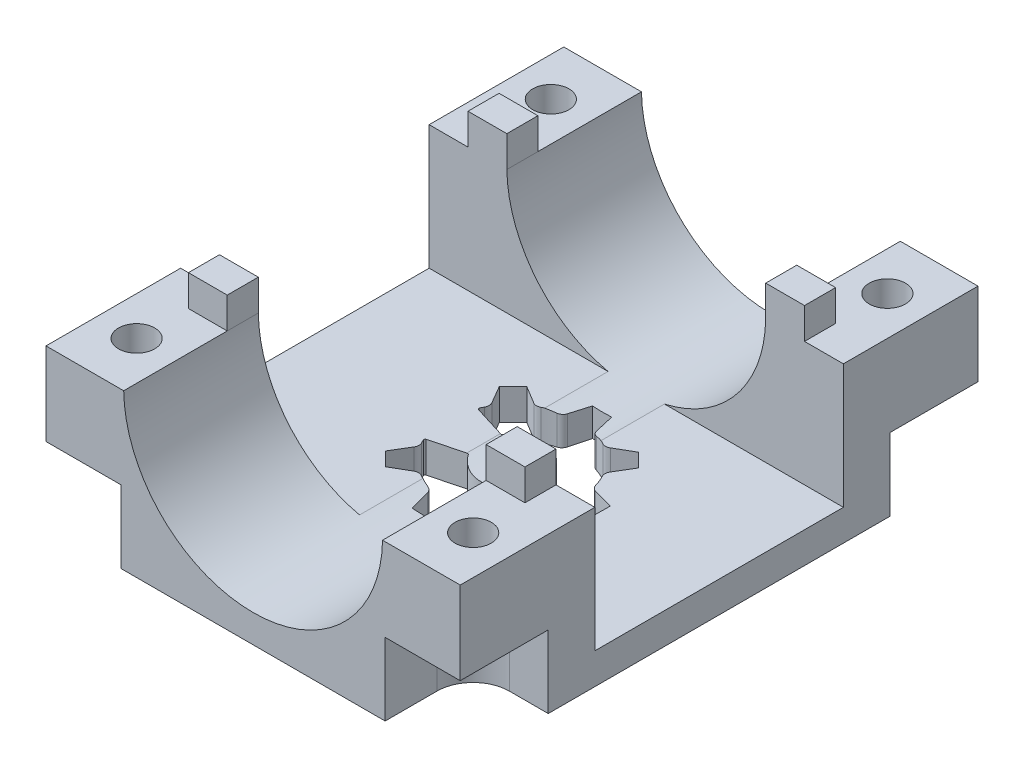
SolidWorks part; units mm, degrees
ref_plane "Alzado" through (0, 0, 0) normal (0, 0, 1) x (1, 0, 0)
ref_plane "Planta" through (0, 0, 0) normal (0, 1, 0) x (1, 0, 0)
ref_plane "Vista lateral" through (0, 0, 0) normal (1, 0, 0) x (0, 0, -1)
sketch "Croquis1" plane through (0, 0, 0) normal (0, 1, 0) x (1, 0, 0)
  line L1 (0, 0) -> (40, 0)
  line L2 (0, 0) -> (0, 50)
  line L3 (0, 50) -> (40, 50)
  line L4 (40, 0) -> (40, 50)
  dimension "D1" = 50
  dimension "D2" = 40
extrude "Saliente-Extruir1" add sketch "Croquis1" along normal blind 20
sketch "Croquis2" plane through (0, 0, 0) normal (0, 0, 1) x (1, 0, 0)
  line L1 (20, 20) -> (20, 20.2) construction
  line L2 (0, 20) -> (40, 20) construction
  circle A1 centre (20, 20.2) radius 12.5
  dimension "D1" = 0.2
  dimension "D2" = 25
extrude "Cortar-Extruir1" cut sketch "Croquis2" against normal through all
sketch "Croquis3" plane through (0, 20, 0) normal (0, 1, 0) x (1, 0, 0)
  line L1 (7.5016, 50) -> (0, 50) construction
  line L6 (0, 50) -> (0, 0) construction
  circle A0 centre (3.75, 45) radius 1.75
  circle A1 centre (36.25, 45) radius 1.75
  circle A2 centre (36.25, 5) radius 1.75
  circle A3 centre (3.75, 5) radius 1.75
  dimension "D1" = 5
  dimension "D5" = 3.5
  dimension "D2" = 3.75
  dimension "D3" = 2
  dimension "D4" = 2
extrude "Cortar-Extruir2" cut sketch "Croquis3" against normal through all
sketch "Croquis4" plane through (40, 0, 0) normal (1, 0, 0) x (0, 0, -1)
  line L2 (0, 20) -> (50, 20) construction
  line L3 (25, 20) -> (37, 20)
  line L4 (37, 20) -> (37, 8)
  line L5 (37, 8) -> (13, 8)
  line L6 (13, 8) -> (13, 20)
  line L7 (13, 20) -> (25, 20)
  dimension "D1" = 12
  dimension "D2" = 12
  dimension "D3" = 24
  dimension "D4" = 12
extrude "Cortar-Extruir3" cut sketch "Croquis4" against normal through all
sketch "Croquis5" plane through (0, 20, 0) normal (0, 1, 0) x (1, 0, 0)
  line L16 (7.5016, 40) -> (7.5016, 37)
  line L17 (3.7508, 37) -> (3.7508, 40)
  line L18 (0, 37) -> (7.5016, 37) construction
  line L19 (3.7508, 40) -> (7.5016, 40)
  line L21 (32.4984, 13) -> (32.4984, 10)
  line L22 (7.5016, 37) -> (3.7508, 37)
  line L23 (36.2492, 37) -> (36.2492, 40)
  line L24 (32.4984, 37) -> (40, 37) construction
  line L25 (36.2492, 40) -> (32.4984, 40)
  line L27 (7.5016, 13) -> (7.5016, 10)
  line L28 (32.4984, 37) -> (36.2492, 37)
  line L29 (36.2492, 13) -> (36.2492, 10)
  line L30 (32.4984, 13) -> (40, 13) construction
  line L31 (36.2492, 10) -> (32.4984, 10)
  line L33 (7.5016, 0) -> (7.5016, 13) construction
  line L34 (32.4984, 13) -> (36.2492, 13)
  line L35 (3.7508, 10) -> (3.7508, 13)
  line L36 (0, 13) -> (7.5016, 13) construction
  line L37 (3.7508, 13) -> (7.5016, 13)
  line L40 (7.5016, 10) -> (3.7508, 10)
  line L42 (32.4984, 40) -> (32.4984, 37)
  line L48 (7.5016, 37) -> (7.5016, 50) construction
  line L50 (32.4984, 50) -> (32.4984, 37) construction
  dimension "D1" = 3
  dimension "D4" = 3
extrude "Saliente-Extruir3" add sketch "Croquis5" along normal blind 3
sketch "Croquis6" plane through (0, 0, 0) normal (0, -1, 0) x (1, 0, 0)
  line L0 (20, 0) -> (20, -50) construction
  line L1 (13.1881, -19.6153) -> (14.5015, -18.2797)
  line L2 (18.9908, -16.3758) -> (20.864, -16.36)
  line L3 (25.3847, -18.1881) -> (26.7203, -19.5015)
  line L4 (28.6242, -23.9908) -> (28.64, -25.864)
  line L5 (26.8119, -30.3847) -> (25.4985, -31.7203)
  line L6 (14.2096, -27.5521) -> (17.384, -26.5714)
  line L7 (13.1881, -19.6153) -> (14.2199, -21.3215)
  line L8 (21.0092, -33.6242) -> (19.136, -33.64)
  line L9 (14.6153, -31.8119) -> (13.2797, -30.4985)
  line L10 (14.5015, -18.2797) -> (16.2249, -19.2826)
  line L11 (18.9908, -16.3758) -> (18.5139, -18.3118)
  line L12 (20.864, -16.36) -> (21.3734, -18.2878)
  line L13 (25.3847, -18.1881) -> (23.6785, -19.2199)
  line L14 (26.7203, -19.5015) -> (25.7174, -21.2249)
  line L15 (28.6242, -23.9908) -> (26.6882, -23.5139)
  line L16 (28.64, -25.864) -> (26.7122, -26.3734)
  line L17 (26.8119, -30.3847) -> (25.7801, -28.6785)
  line L18 (25.4985, -31.7203) -> (23.7751, -30.7174)
  line L19 (21.0092, -33.6242) -> (21.4861, -31.6882)
  line L20 (19.136, -33.64) -> (18.6266, -31.7122)
  line L21 (14.6153, -31.8119) -> (16.3215, -30.7801)
  line L22 (13.2797, -30.4985) -> (14.2826, -28.7751)
  line L23 (17.4066, -23.3915) -> (14.1706, -22.5477)
  line L24 (0, 0) -> (40, 0) construction
  line L26 (40, -50) -> (0, -50) construction
  line L27 (40, -25) -> (0, -25) construction
  line L28 (40, 0) -> (40, -50) construction
  line L29 (0, -50) -> (0, 0) construction
  arc A0 (21.9667, -31.1744) -> (23.0717, -30.7057) centre (20, -25) ccw
  arc A1 (14.127, -27.7383) -> (14.2943, -28.0717) centre (20, -25) ccw
  arc A2 (14.2096, -27.5521) -> (14.127, -27.7383) centre (14.2495, -27.6812) ccw
  arc A3 (14.0813, -22.3619) -> (14.1706, -22.5477) centre (14.2047, -22.4169) ccw
  arc A4 (16.9283, -19.2943) -> (16.2249, -19.2826) centre (16.587, -18.6603) cw
  arc A5 (14.2434, -22.0247) -> (14.2199, -21.3215) centre (13.6038, -21.6941) ccw
  arc A6 (21.8625, -18.7934) -> (21.3734, -18.2878) centre (22.0695, -18.1038) cw
  arc A7 (18.0333, -18.8256) -> (18.5139, -18.3118) centre (17.8148, -18.1396) ccw
  arc A8 (25.7057, -21.9283) -> (25.7174, -21.2249) centre (26.3397, -21.587) cw
  arc A9 (22.9753, -19.2434) -> (23.6785, -19.2199) centre (23.3059, -18.6038) ccw
  arc A10 (26.2066, -26.8625) -> (26.7122, -26.3734) centre (26.8962, -27.0695) cw
  arc A11 (26.1744, -23.0333) -> (26.6882, -23.5139) centre (26.8604, -22.8148) ccw
  arc A12 (23.0717, -30.7057) -> (23.7751, -30.7174) centre (23.413, -31.3397) cw
  arc A13 (25.7566, -27.9753) -> (25.7801, -28.6785) centre (26.3962, -28.3059) ccw
  arc A14 (18.1375, -31.2066) -> (18.6266, -31.7122) centre (17.9305, -31.8962) cw
  arc A15 (21.9667, -31.1744) -> (21.4861, -31.6882) centre (22.1852, -31.8604) ccw
  arc A16 (14.2943, -28.0717) -> (14.2826, -28.7751) centre (13.6603, -28.413) cw
  arc A17 (17.0247, -30.7566) -> (16.3215, -30.7801) centre (16.6941, -31.3962) ccw
  arc A18 (17.0247, -30.7566) -> (18.1375, -31.2066) centre (20, -25) ccw
  arc A19 (14.2434, -22.0247) -> (14.0813, -22.3619) centre (20, -25) ccw
  arc A20 (18.0333, -18.8256) -> (16.9283, -19.2943) centre (20, -25) ccw
  arc A21 (22.9753, -19.2434) -> (21.8625, -18.7934) centre (20, -25) ccw
  arc A22 (26.1744, -23.0333) -> (25.7057, -21.9283) centre (20, -25) ccw
  arc A23 (25.7566, -27.9753) -> (26.2066, -26.8625) centre (20, -25) ccw
  arc A24 (17.384, -26.5714) -> (17.4066, -23.3915) centre (20, -25) ccw
  dimension "D1" = 0.1351
  dimension "D2" = 0.1351
extrude "Cortar-Extruir5" cut sketch "Croquis6" against normal through all
sketch "Croquis7" plane through (0, 0, 0) normal (0, -1, 0) x (1, 0, 0)
  line L0 (7.25, -5) -> (7.25, 0)
  line L1 (3.75, -8.5) -> (0, -8.5)
  line L2 (0, -50) -> (0, 0) construction
  line L3 (0, -8.5) -> (0, 0)
  line L4 (0, 0) -> (7.25, 0)
  line L6 (32.75, -5) -> (32.75, 0)
  line L7 (0, 0) -> (40, 0) construction
  line L8 (32.75, 0) -> (40, 0)
  line L9 (40, 0) -> (40, -8.5)
  line L10 (40, 0) -> (40, -50) construction
  line L11 (40, -8.5) -> (36.25, -8.5)
  line L12 (36.25, -41.5) -> (40, -41.5)
  line L13 (40, -41.5) -> (40, -50)
  line L14 (40, -50) -> (32.75, -50)
  line L15 (40, -50) -> (0, -50) construction
  line L16 (32.75, -50) -> (32.75, -45)
  line L17 (7.25, -45) -> (7.25, -50)
  line L18 (7.25, -50) -> (0, -50)
  line L19 (0, -50) -> (0, -41.5)
  line L20 (0, -41.5) -> (3.75, -41.5)
  arc A0 (3.75, -8.5) -> (7.25, -5) centre (3.75, -5) ccw
  arc A1 (32.75, -5) -> (36.25, -8.5) centre (36.25, -5) ccw
  arc A2 (36.25, -41.5) -> (32.75, -45) centre (36.25, -45) ccw
  arc A3 (7.25, -45) -> (3.75, -41.5) centre (3.75, -45) ccw
  dimension "D1" = 7
  dimension "D2" = 7
  dimension "D3" = 7
  dimension "D4" = 7
extrude "Cortar-Extruir6" cut sketch "Croquis7" against normal blind 12
sketch "Croquis8" plane through (0, 0, 0) normal (0, -1, 0) x (1, 0, 0)
  line L1 (0, 0) -> (40, 0)
  line L2 (0, 0) -> (0, -50)
  line L3 (0, -50) -> (40, -50)
  line L4 (40, 0) -> (40, -50)
extrude "Cortar-Extruir7" cut sketch "Croquis8" against normal blind 5
